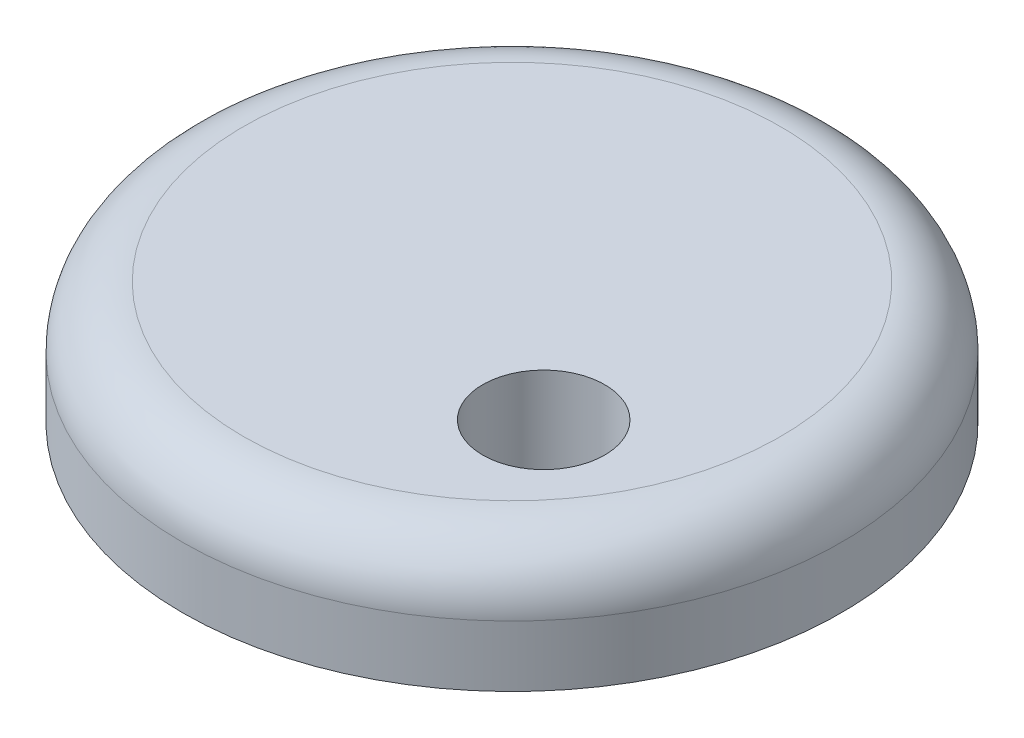
SolidWorks part; units mm, degrees
material "ABS"
ref_plane "Front Plane" through (0, 0, 0) normal (0, 0, 1) x (1, 0, 0)
ref_plane "Top Plane" through (0, 0, 0) normal (0, 1, 0) x (1, 0, 0)
ref_plane "Right Plane" through (0, 0, 0) normal (1, 0, 0) x (0, 0, -1)
sketch "Sketch1" plane through (0, 0, 0) normal (0, 1, 0) x (1, 0, 0)
  circle A0 centre (0, 0) radius 27
  dimension "D1" = 54
extrude "Boss-Extrude1" add sketch "Sketch1" along normal blind 10
fillet "Fillet1" radius 5 1 edges at (0, 10, 27)
sketch "Sketch2" plane through (0, 10, 0) normal (0, 1, 0) x (1, 0, 0)
  circle A0 centre (11.1127, -8.5152) radius 5
  circle A1 centre (0, 0) radius 22 construction
  dimension "D1" = 10
  dimension "D2" = 14
  dimension "D3" = 11.1127
extrude "Cut-Extrude1" cut sketch "Sketch2" against normal blind 10
